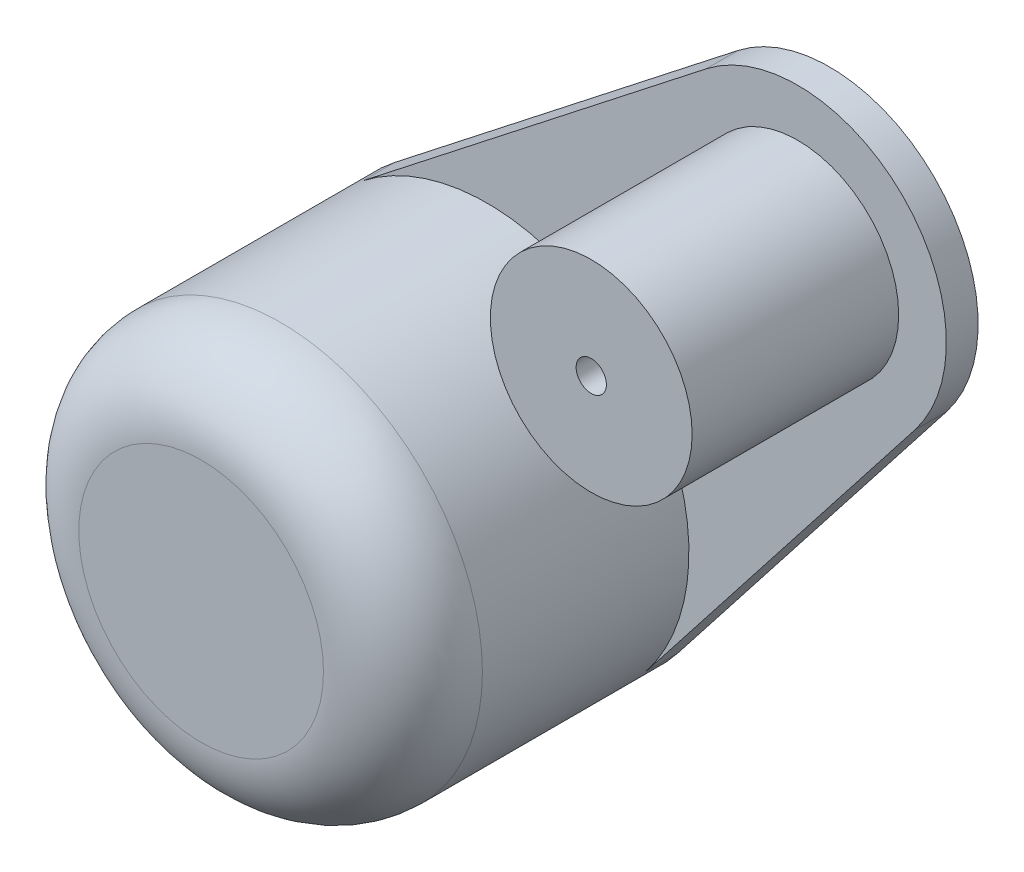
SolidWorks part; units mm, degrees
ref_plane "Front Plane" through (0, 0, 0) normal (0, 0, 1) x (1, 0, 0)
ref_plane "Top Plane" through (0, 0, 0) normal (0, 1, 0) x (1, 0, 0)
ref_plane "Right Plane" through (0, 0, 0) normal (1, 0, 0) x (0, 0, -1)
sketch "Sketch1" plane through (0, 0, 0) normal (0, 0, 1) x (1, 0, 0)
  circle A0 centre (0, 0) radius 12.7
  dimension "D1" = 25.4
extrude "Boss-Extrude1" add sketch "Sketch1" along normal blind 20
ref_axis "Axis1" through (0, 0, -1) along (0, 0, 1)
sketch "Sketch2" plane through (0, 0, 0) normal (0, 1, 0) x (1, 0, 0)
  line L0 (0, 0) -> (0, -17.175)
  line L1 (0, -17.175) -> (3.175, -14)
  line L2 (3.175, -14) -> (3.175, 0)
  line L3 (12.7, 0) -> (-12.7, 0) construction
  line L4 (3.175, 0) -> (0, 0)
  dimension "D1" = 14
  dimension "D2" = 135
  dimension "D3" = 3.175
revolve "Cut-Revolve1" cut sketch "Sketch2" angle 360 about axis through (0, 0, -1) along (0, 0, 1)
fillet "Fillet1" radius 5 1 edges at (12.7, 0, 20)
sketch "Sketch3" plane through (0, 0, 0) normal (0, 1, 0) x (1, 0, 0)
  line L0 (0, 1) -> (0, -21) construction
  line L1 (12.7, 0) -> (-12.7, 0) construction
  circle A0 centre (0, -6) radius 2.4257
  dimension "D1" = 4.8514
  dimension "D2" = 6
extrude "Cut-Extrude1" cut sketch "Sketch3" against normal up to next
sketch "Sketch4" plane through (0, 0, 0) normal (1, 0, 0) x (0, 0, -1)
  line L0 (1, 0) -> (-21, 0) construction
  line L1 (0, -12.7) -> (0, 12.7) construction
  circle A0 centre (-6, 0) radius 2.4257
  dimension "D1" = 4.8514
  dimension "D2" = 6
extrude "Cut-Extrude2" cut sketch "Sketch4" against normal up to next
sketch "Sketch5" plane through (0, 0, 0) normal (0, 0, 1) x (1, 0, 0)
  line L0 (0, 0) -> (26.163, 26.163) construction
  line L1 (0, 0) -> (46.8191, 0) construction
  line L2 (13.7898, 26.9153) -> (-7.8261, 10.0021)
  line L3 (26.9153, 13.7898) -> (10.0021, -7.8261)
  arc A0 (26.9153, 13.7898) -> (13.7898, 26.9153) centre (19.5515, 19.5515) ccw
  arc A1 (10.0021, -7.8261) -> (-7.8261, 10.0021) centre (0, 0) ccw
  circle A4 centre (0, 0) radius 12.7 construction
  dimension "D3" = 18.7
  dimension "D1" = 45
  dimension "D2" = 37
extrude "Boss-Extrude2" add sketch "Sketch5" along normal blind 2
sketch "Sketch6" plane through (0, 0, 2) normal (0, 0, 1) x (1, 0, 0)
  circle A0 centre (19.5515, 19.5515) radius 6.35
  dimension "D1" = 12.7
extrude "Boss-Extrude3" add sketch "Sketch6" along normal offset from surface (13 mm away) 15 up to face at (-3.175, 0, 0)
ref_axis "Axis2" through (19.5515, 19.5515, 15) along (0, 0, -1)
ref_plane "Plane1" through (0, 0, 0) normal (-0.7071, 0.7071, 0) x (0, 0, 1)
sketch "Sketch7" plane through (0, 0, 0) normal (-0.7071, 0.7071, 0) x (0, 0, 1)
  line L0 (0, 30.65) -> (4, 30.65)
  line L1 (0, 37) -> (0, 28.7828) construction
  line L2 (4, 30.65) -> (7, 27.65)
  line L3 (15, 27.65) -> (2, 27.65) construction
  line L4 (7, 27.65) -> (0, 27.65)
  line L5 (0, 28.7828) -> (0, 1.5387) construction
  line L6 (0, 27.65) -> (0, 30.65)
  dimension "D1" = 7
  dimension "D2" = 45
  dimension "D3" = 3
revolve "Cut-Revolve2" cut sketch "Sketch7" angle 360 about axis through (19.5515, 19.5515, 15) along (0, 0, -1)
sketch "Sketch8" plane through (0, 0, 15) normal (0, 0, 1) x (1, 0, 0)
  circle A1 centre (19.5515, 19.5515) radius 0.9525
  dimension "D1" = 1.905
extrude "Cut-Extrude3" cut sketch "Sketch8" against normal through all
